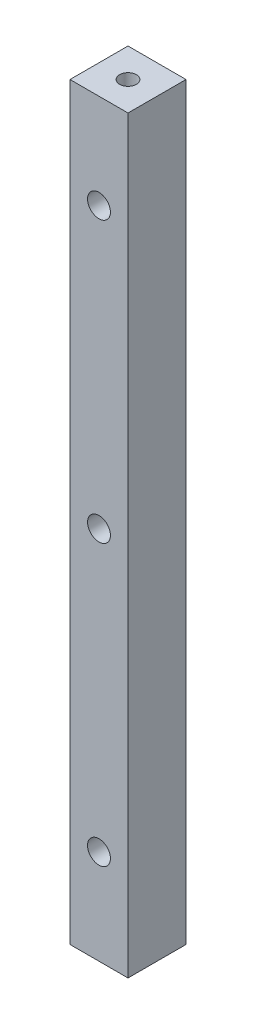
SolidWorks part; units mm, degrees
ref_plane "Plan de face" through (0, 0, 0) normal (0, 0, 1) x (1, 0, 0)
ref_plane "Plan de dessus" through (0, 0, 0) normal (0, 1, 0) x (1, 0, 0)
ref_plane "Plan de droite" through (0, 0, 0) normal (1, 0, 0) x (0, 0, -1)
sketch "Esquisse1" plane through (0, 0, 0) normal (0, 1, 0) x (1, 0, 0)
  line L1 (-5.7, 5.7) -> (5.7, 5.7)
  line L2 (-5.7, 5.7) -> (-5.7, -5.7)
  line L3 (-5.7, -5.7) -> (5.7, -5.7)
  line L4 (5.7, 5.7) -> (5.7, -5.7)
  line L5 (-5.7, 5.7) -> (5.7, -5.7) construction
  line L6 (-5.7, -5.7) -> (5.7, 5.7) construction
  point P0 (0, 0)
  dimension "D1" = 11.4
  dimension "D2" = 11.4
extrude "Boss.-Extru.1" add sketch "Esquisse1" along normal blind 147.2
hole_wizard "Trou taraudé M41" positions "Esquisse3" profile "Esquisse2" tap size "M4" standard "ISO"
sketch "Esquisse3" plane through (0, 147.2, 0) normal (0, 1, 0) x (-1, 0, 0)
  point P1 (0, 0)
sketch "Esquisse2" plane through (0, 147.2, 0) normal (1, 0, 0) x (0, 0, 1)
  line L0 (0, 0) -> (0, 12.4914)
  line L1 (0, 12.4914) -> (1.65, 11.5)
  line L2 (1.65, 11.5) -> (1.65, 0)
  line L5 (1.65, 0) -> (0, 0)
  line L10 (0, 12.4914) -> (-1.65, 11.5) construction
  line L11 (0, -6.35) -> (0, 107.95) construction
  dimension "Diamètre du trou pour taraudage" = 3.3
  dimension "Profondeur du trou pour taraudage" = 11.5
  dimension "Angle de pointe" = 118
cosmetic thread "Filetage de perçage1" parameters "D1"=8, "D2"=4
hole_wizard "Trou taraudé M42" positions "Esquisse5" profile "Esquisse4" tap size "M4" standard "ISO"
sketch "Esquisse5" plane through (0, 0, 0) normal (0, -1, 0) x (1, 0, 0)
  point P1 (0, 0)
sketch "Esquisse4" plane through (0, 0, 0) normal (1, 0, 0) x (0, 0, -1)
  line L0 (0, 0) -> (0, 12.4914)
  line L1 (0, 12.4914) -> (1.65, 11.5)
  line L2 (1.65, 11.5) -> (1.65, 0)
  line L5 (1.65, 0) -> (0, 0)
  line L10 (0, 12.4914) -> (-1.65, 11.5) construction
  line L11 (0, -6.35) -> (0, 107.95) construction
  dimension "Diamètre du trou pour taraudage" = 3.3
  dimension "Profondeur du trou pour taraudage" = 11.5
  dimension "Angle de pointe" = 118
cosmetic thread "Filetage de perçage2" parameters "D1"=8, "D2"=4
sketch "Esquisse6" plane through (0, 0, 5.7) normal (0, 0, 1) x (1, 0, 0)
  line L0 (-5.7, 0) -> (5.7, 0) construction
  line L1 (5.7, 147.2) -> (5.7, 0) construction
  point P0 (0, 18.6)
  point P1 (0, 73.6)
  point P2 (0, 128.6)
  dimension "D1" = 55
  dimension "D2" = 55
  dimension "D3" = 73.6
  dimension "D4" = 5.7
  dimension "D5" = 5.7
  dimension "D6" = 5.7
hole_wizard "Dégagement M41" positions "Esquisse8" profile "Esquisse7" hole size "M4" standard "ISO" end condition through all
sketch "Esquisse8" plane through (0, 0, 5.7) normal (0, 0, 1) x (1, 0, 0)
  point P1 (0, 128.6)
  point P4 (0, 73.6)
  point P7 (0, 18.6)
sketch "Esquisse7" plane through (0, 128.6, 5.7) normal (1, 0, 0) x (0, -1, 0)
  line L0 (0, 0) -> (0, 11.4)
  line L1 (0, 11.4) -> (2.25, 11.4)
  line L2 (2.25, 11.4) -> (2.25, 0)
  line L5 (2.25, 0) -> (0, 0)
  line L11 (0, -6.35) -> (0, 107.95) construction
  dimension "Diamètre du perçage jusqu'au prochain" = 4.5
  dimension "Profondeur du perçage jusqu'au prochain" = 11.4
